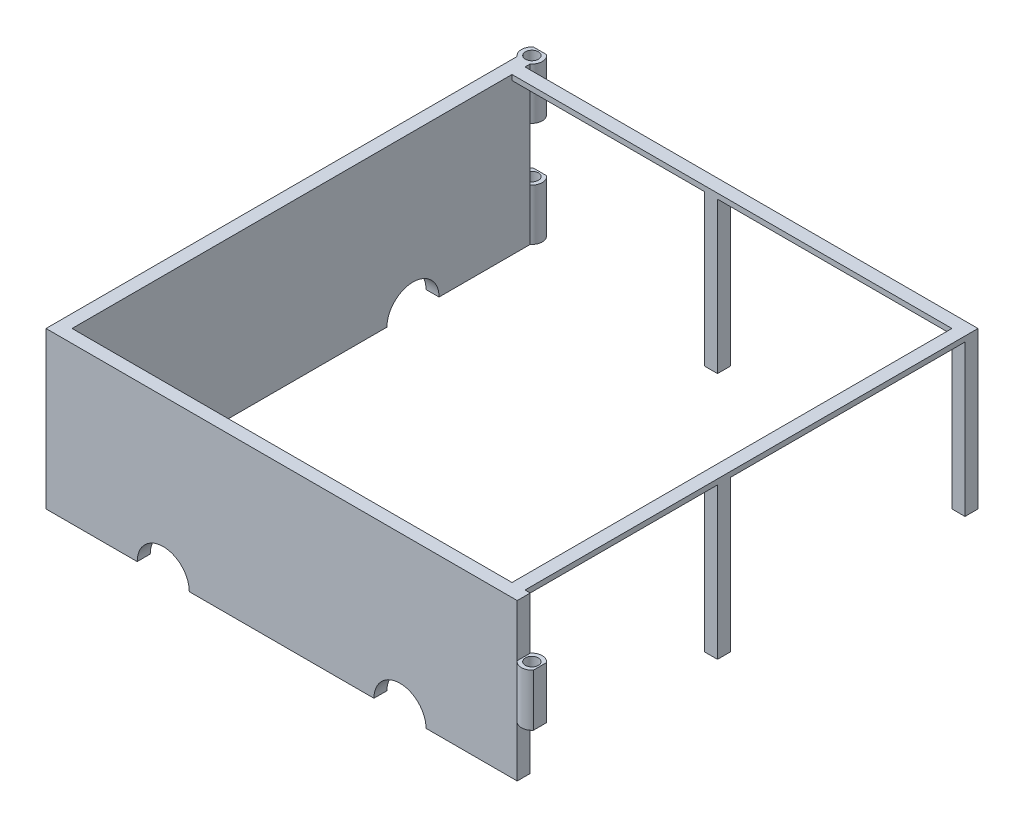
SolidWorks part; units mm, degrees
ref_plane "Front Plane" through (0, 0, 0) normal (0, 0, 1) x (1, 0, 0)
ref_plane "Top Plane" through (0, 0, 0) normal (0, 1, 0) x (1, 0, 0)
ref_plane "Right Plane" through (0, 0, 0) normal (1, 0, 0) x (0, 0, -1)
sketch "Sketch1" plane through (0, 0, 0) normal (0, 1, 0) x (1, 0, 0)
  line L0 (0, 0) -> (180, 0)
  line L1 (0, 0) -> (0, 180)
  line L3 (5, 180) -> (5, 5)
  line L4 (5, 5) -> (180, 5)
  line L6 (180, 5) -> (180.8775, 5)
  line L7 (180, 0) -> (180.8775, 0)
  line L8 (5, 180) -> (5, 180.8775)
  line L9 (0, 180) -> (0, 180.8775)
  arc A0 (180.8775, 0) -> (180.8775, 5) centre (184, 2.5) ccw
  arc A1 (5, 180.8775) -> (0, 180.8775) centre (2.5, 184) ccw
  dimension "D6" = 4
  dimension "D9" = 4
  dimension "D12" = 2.5
  dimension "D1" = 180
  dimension "D2" = 180
  dimension "D3" = 5
  dimension "D4" = 5
  dimension "D5" = 0.8775
  dimension "D7" = 0.8775
  dimension "D8" = 3.1225
  dimension "D10" = 0.8775
  dimension "D11" = 0.8775
extrude "Boss-Extrude1" add sketch "Sketch1" along normal blind 60
sketch "Sketch2" plane through (0, 60, 0) normal (0, 1, 0) x (1, 0, 0)
  circle A0 centre (184, 2.5) radius 2.5
  circle A1 centre (2.5, 184) radius 2.5
  dimension "D1" = 5
  dimension "D2" = 5
extrude "Cut-Extrude1" cut sketch "Sketch2" against normal blind 60
sketch "Sketch4" plane through (0, 0, 0) normal (0, 0, 1) x (1, 0, 0)
  line L0 (180.8775, 0) -> (188, 0)
  line L1 (188, 0) -> (188, 20)
  line L2 (188, 0) -> (188, 60) construction
  line L3 (188, 20) -> (180.8775, 20)
  line L4 (180.8775, 60) -> (180.8775, 0) construction
  line L5 (180.8775, 20) -> (180.8775, 0)
  line L6 (180.8775, 60) -> (188, 60)
  line L7 (188, 60) -> (188, 40)
  line L8 (188, 40) -> (180.8775, 40)
  line L9 (180.8775, 40) -> (180.8775, 60)
  line L10 (180.8775, 0) -> (135.8775, 0)
  line L11 (0, 0) -> (180.8775, 0) construction
  line L12 (0, 0) -> (45, 0)
  circle A0 centre (135.8775, 0) radius 10
  circle A1 centre (45, 0) radius 10
  line M7 (0, 0) -> (180.8775, 0)
  line M8 (180.8775, 0) -> (180.8775, 60)
  dimension "D4" = 20
  dimension "D6" = 20
  dimension "D1" = 20
  dimension "D2" = 20
  dimension "D3" = 45
  dimension "D5" = 45
extrude "Cut-Extrude3" cut sketch "Sketch4" against normal through all both and the other way through all contours A1 L12 M7 | A0 M7 | L1 L3 L0 M8 | L8 L7 L6 M8
sketch "Sketch5" plane through (0, 40, 0) normal (0, 1, 0) x (1, 0, 0)
  line L0 (181.5, 2.5) -> (180.8775, 2.5)
  line L1 (180.8775, 5) -> (180.8775, 0) construction
  line L2 (186.5, 2.5) -> (187.1225, 2.5)
  line L3 (187.1225, 2.5) -> (187.1225, 5)
  line L4 (187.1225, 5) -> (188.4607, 5)
  line L5 (188.4607, 5) -> (188.4607, -0.6564)
  line L6 (188.4607, -0.6564) -> (187.1225, -0.6564)
  line L7 (187.1225, -0.6564) -> (187.1225, 2.5)
  circle A0 centre (184, 2.5) radius 2.5 construction
  arc A1 (180.8775, 0) -> (180.8775, 5) centre (184, 2.5) ccw construction
  arc M9 (180.8775, 0) -> (180.8775, 5) centre (184, 2.5) ccw
  dimension "D1" = 5.6564
  dimension "D2" = 1.3382
extrude "Cut-Extrude4" cut sketch "Sketch5" against normal through all both contours L7 L3 M9
sketch "Sketch6" plane through (0, 0, 0) normal (-1, 0, 0) x (0, 0, 1)
  line L0 (0, 0) -> (-45, 0)
  line L1 (-180.8775, 0) -> (0, 0) construction
  line L2 (-180.8775, 0) -> (-135.8775, 0)
  line L3 (-180.8775, 0) -> (-180.8775, 19.75)
  line L4 (-180.8775, 60) -> (-180.8775, 0) construction
  line L5 (-180.8775, 19.75) -> (-180.8775, 40.25)
  line L6 (-180.8775, 40.25) -> (-189.3831, 40.25)
  line L7 (-189.3831, 40.25) -> (-189.3831, 19.75)
  line L8 (-189.3831, 19.75) -> (-180.8775, 19.75)
  circle A0 centre (-45, 0) radius 10
  circle A1 centre (-135.8775, 0) radius 10
  line M6 (-180.8775, 0) -> (0, 0)
  line M9 (-180.8775, 60) -> (-180.8775, 0)
  dimension "D2" = 20
  dimension "D4" = 20
  dimension "D1" = 45
  dimension "D3" = 45
  dimension "D5" = 20.5
  dimension "D6" = 19.75
  dimension "D7" = 8.5056
extrude "Cut-Extrude6" cut sketch "Sketch6" against normal through all both and the other way through all contours A1 L2 M6 | A0 M6 | L7 L8 L6 M9
sketch "Sketch7" plane through (0, 60, 0) normal (0, 1, 0) x (1, 0, 0)
  line L0 (0, 180.8775) -> (5, 180.8775)
  line L1 (5, 5) -> (5, 180.8775) construction
  line L2 (2.5, 180.8775) -> (2.5, 181.5)
  line L4 (2.5, 187.1225) -> (5.6708, 187.1225)
  line L5 (5.6708, 187.1225) -> (5.6708, 188.6509)
  line L6 (5.6708, 188.6509) -> (0, 188.6509)
  line L7 (0, 188.6509) -> (-0.7692, 188.6509)
  line L8 (-0.7692, 188.6509) -> (-0.7692, 187.1225)
  line L9 (-0.7692, 187.1225) -> (2.5, 187.1225)
  arc A0 (5, 180.8775) -> (0, 180.8775) centre (2.5, 184) ccw construction
  circle A1 centre (2.5, 184) radius 2.5 construction
  arc M14 (5, 180.8775) -> (0, 180.8775) centre (2.5, 184) ccw
  dimension "D1" = 1.5284
  dimension "D2" = 5.6708
  dimension "D3" = 6.245
  dimension "D4" = 0.7692
  dimension "D5" = 3.2692
  dimension "D6" = 5.6225
extrude "Cut-Extrude7" cut sketch "Sketch7" against normal through all both contours L9 L4 M14
sketch "Sketch8" plane through (0, 60, 0) normal (0, 1, 0) x (1, 0, 0)
  line L0 (5, 180.8775) -> (5, 178.8775)
  line L1 (5, 5) -> (5, 180.8775) construction
  line L2 (5, 178.8775) -> (178.8775, 178.8775)
  line L3 (180.8775, 5) -> (178.8775, 5)
  line L4 (180.8775, 5) -> (5, 5) construction
  line L5 (178.8775, 5) -> (178.8775, 178.8775)
  line L6 (178.8775, 5) -> (173.8775, 5)
  line L7 (173.8775, 5) -> (173.8775, 173.8775)
  line L8 (173.8775, 173.8775) -> (5, 173.8775)
  line M11 (180.8775, 5) -> (5, 5)
  line M12 (5, 5) -> (5, 180.8775)
  dimension "D1" = 2
  dimension "D2" = 2
  dimension "D3" = 5
  dimension "D4" = 5
extrude "Boss-Extrude2" add sketch "Sketch8" against normal blind 2 contours L8 L7 L5 L2 M11 M12
sketch "Sketch9" plane through (0, 58, 0) normal (0, -1, 0) x (-1, 0, 0)
  line L0 (-173.8775, 173.8775) -> (-178.8775, 173.8775)
  line L1 (-178.8775, 5) -> (-178.8775, 178.8775) construction
  line L2 (-178.8775, 173.8775) -> (-178.8775, 178.8775)
  line L3 (-178.8775, 178.8775) -> (-173.8775, 178.8775)
  line L4 (-5, 178.8775) -> (-178.8775, 178.8775) construction
  line L5 (-173.8775, 178.8775) -> (-173.8775, 173.8775)
  line L6 (-178.8775, 78.8775) -> (-173.8775, 78.8775)
  line L7 (-173.8775, 5) -> (-173.8775, 173.8775) construction
  line L8 (-173.8775, 78.8775) -> (-173.8775, 83.8775)
  line L9 (-173.8775, 83.8775) -> (-178.8775, 83.8775)
  line L10 (-178.8775, 83.8775) -> (-178.8775, 78.8775)
  line L12 (-78.8775, 173.8775) -> (-78.8775, 178.8775)
  line L13 (-173.8775, 173.8775) -> (-5, 173.8775) construction
  line L14 (-78.8775, 178.8775) -> (-83.8775, 178.8775)
  line L15 (-83.8775, 178.8775) -> (-83.8775, 173.8775)
  line L16 (-83.8775, 173.8775) -> (-78.8775, 173.8775)
  dimension "D1" = 5
  dimension "D2" = 90
  dimension "D3" = 5
  dimension "D4" = 90
extrude "Boss-Extrude3" add sketch "Sketch9" along normal blind 58
